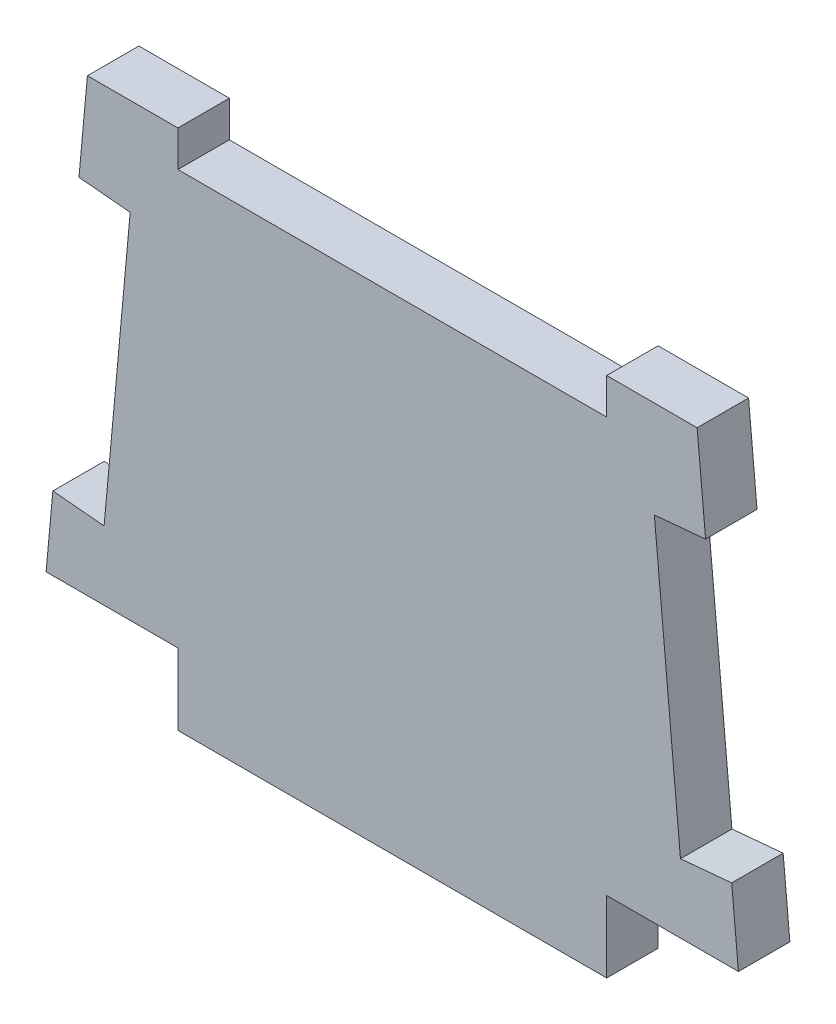
SolidWorks part; units mm, degrees
ref_plane "Front Plane" through (0, 0, 0) normal (0, 0, 1) x (1, 0, 0)
ref_plane "Top Plane" through (0, 0, 0) normal (0, 1, 0) x (1, 0, 0)
ref_plane "Right Plane" through (0, 0, 0) normal (1, 0, 0) x (0, 0, -1)
sketch "Sketch1" plane through (0, 0, 0) normal (0, 0, 1) x (1, 0, 0)
  line L1 (-27.0891, 18.738) -> (27.0891, 18.738)
  line L2 (-27.0891, 18.738) -> (-30.7594, -21.2768)
  line L3 (-30.7594, -21.2768) -> (30.7594, -21.2768)
  line L4 (27.0891, 18.738) -> (30.7594, -21.2768)
  line L5 (-27.0891, 18.738) -> (30.7594, -21.2768) construction
  line L6 (-30.7594, -21.2768) -> (27.0891, 18.738) construction
  point P0 (0, 0)
  dimension "D1" = 40.1828
  dimension "D5" = 54.1782
  dimension "D6" = 61.5188
extrude "Boss-Extrude1" add sketch "Sketch1" along normal blind 4.572
sketch "Sketch2" plane through (0, 0, 4.572) normal (0, 0, 1) x (1, 0, 0)
  line L0 (27.0891, 18.738) -> (-27.0891, 18.738) construction
  line L6 (19.05, 18.738) -> (-19.05, 18.738)
  line L7 (19.05, 18.738) -> (19.05, 15.5376)
  line L8 (19.05, 15.5376) -> (-19.05, 15.5376)
  line L9 (-19.05, 18.738) -> (-19.05, 15.5376)
  line L10 (-30.1608, -14.751) -> (-27.8408, 10.5428)
  line L11 (-30.1608, -14.751) -> (-25.6079, -15.1686)
  line L12 (-27.8408, 10.5428) -> (-23.2879, 10.1252)
  line L13 (-25.6079, -15.1686) -> (-23.2879, 10.1252)
  line L14 (-27.0891, 18.738) -> (-30.7594, -21.2768) construction
  line L15 (27.8408, 10.5428) -> (30.1608, -14.751)
  line L16 (27.8408, 10.5428) -> (23.2879, 10.1252)
  line L17 (30.1608, -14.751) -> (25.6079, -15.1686)
  line L18 (23.2879, 10.1252) -> (25.6079, -15.1686)
  line L19 (30.7594, -21.2768) -> (27.0891, 18.738) construction
  point P1 (0, 18.738)
  point P2 (-29.0008, -2.1041)
  point P3 (-28.9242, -1.2694)
  dimension "D1" = 3.2004
  dimension "D2" = 38.1
  dimension "D3" = 25.4
  dimension "D4" = 4.572
  dimension "D5" = 0.8382
extrude "Cut-Extrude1" cut sketch "Sketch2" against normal through all
sketch "Sketch3" plane through (0, 0, 4.572) normal (0, 0, 1) x (1, 0, 0)
  line L0 (-30.7594, -21.2768) -> (30.7594, -21.2768) construction
  line L1 (-19.05, -21.2768) -> (19.05, -21.2768)
  line L2 (-19.05, -21.2768) -> (-19.05, -27.6268)
  line L3 (-19.05, -27.6268) -> (19.05, -27.6268)
  line L4 (19.05, -21.2768) -> (19.05, -27.6268)
  point P6 (0, -21.2768)
  dimension "D1" = 6.35
  dimension "D2" = 38.1
extrude "Boss-Extrude2" add sketch "Sketch3" against normal up to surface (4.572 mm away) up to face at (0, 2.8106, 0)
